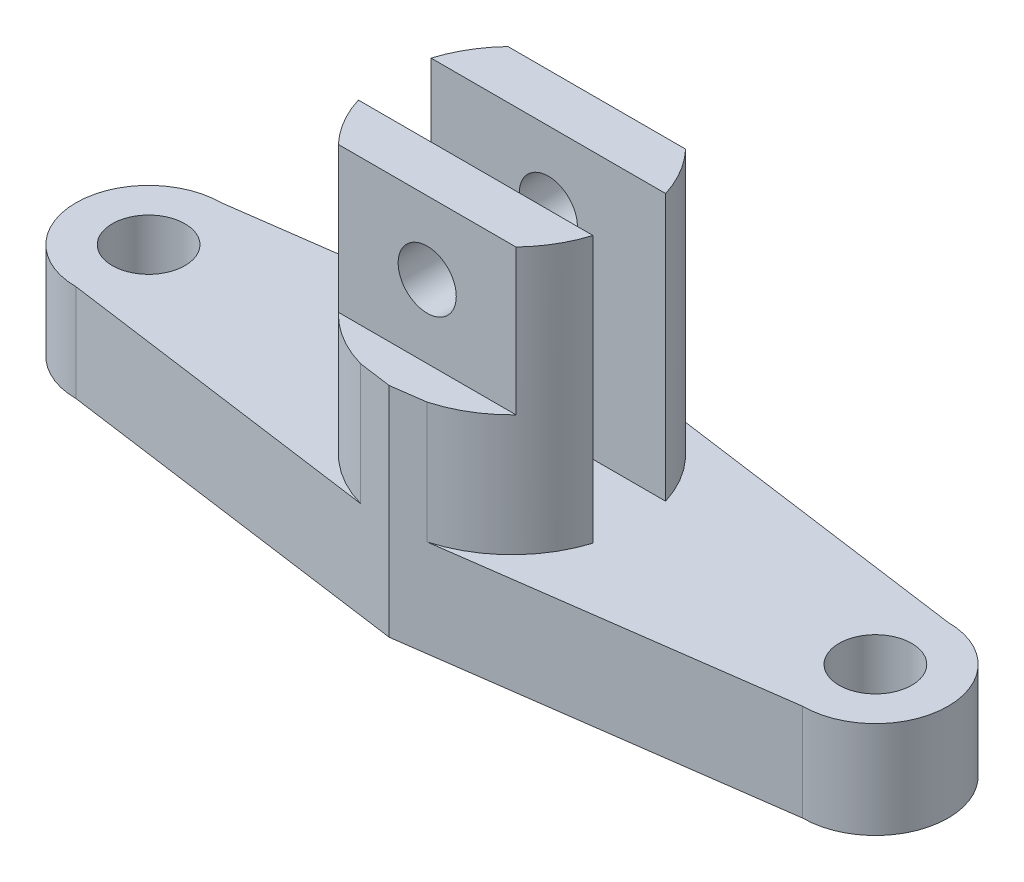
SolidWorks part; units mm, degrees
ref_plane "Alzado" through (0, 0, 0) normal (0, 0, 1) x (1, 0, 0)
ref_plane "Planta" through (0, 0, 0) normal (0, 1, 0) x (1, 0, 0)
ref_plane "Vista lateral" through (0, 0, 0) normal (1, 0, 0) x (0, 0, -1)
sketch "Croquis Planta" plane through (0, 0, 0) normal (0, 1, 0) x (1, 0, 0)
  line L0 (75, 15) -> (0, 25.3396)
  line L1 (0, 25.3396) -> (-75, 15)
  line L2 (0, -25.3396) -> (-75, -15)
  line L3 (0, -25.3396) -> (75, -15)
  circle A0 centre (0, 0) radius 25.3396
  circle A1 centre (75, 0) radius 7.5
  circle A2 centre (-75, 0) radius 7.5
  arc A3 (75, -15) -> (75, 15) centre (75, 0) ccw
  arc A4 (-75, 15) -> (-75, -15) centre (-75, 0) ccw
extrude "Saliente-Extruir1" add sketch "Croquis Planta" along normal blind 20 contours L1 A4 L2 A0 A2 | L3 A3 L0 A0 A1 | L3 A0 L0 L1 L2
sketch "Croquis11" plane through (0, 0, 0) normal (0, 1, 0) x (1, 0, 0)
  line L0 (75, 15) -> (0, 25.3396)
  line L1 (0, 25.3396) -> (-75, 15)
  line L2 (0, -25.3396) -> (-75, -15)
  line L3 (0, -25.3396) -> (75, -15)
  line L4 (-24.2042, 7.5) -> (24.2042, 7.5)
  line L5 (18.326, 17.5) -> (-18.326, 17.5)
  line L6 (-24.2042, -7.5) -> (24.2042, -7.5)
  line L7 (18.326, -17.5) -> (-18.326, -17.5)
  arc A0 (-24.2042, -7.5) -> (24.2042, -7.5) centre (0, 0) ccw
  circle A1 centre (75, 0) radius 7.5
  circle A2 centre (-75, 0) radius 7.5
  arc A3 (75, -15) -> (75, 15) centre (75, 0) ccw
  arc A4 (-75, 15) -> (-75, -15) centre (-75, 0) ccw
  arc A5 (24.2042, 7.5) -> (-24.2042, 7.5) centre (0, 0) ccw
extrude "Saliente-Extruir2" add sketch "Croquis11" along normal blind 45 contours L4 A5 L5 | L5 A5 L0 L1 | L7 A0 L6 | L3 A0 L7 L2
sketch "Croquis12" plane through (0, 0, 0) normal (0, 1, 0) x (1, 0, 0)
  line L0 (75, 15) -> (0, 25.3396)
  line L1 (0, 25.3396) -> (-75, 15)
  line L2 (0, -25.3396) -> (-75, -15)
  line L3 (0, -25.3396) -> (75, -15)
  line L4 (-24.2042, 7.5) -> (24.2042, 7.5)
  line L5 (18.326, 17.5) -> (-18.326, 17.5)
  line L6 (-24.2042, -7.5) -> (24.2042, -7.5)
  line L7 (18.326, -17.5) -> (-18.326, -17.5)
  arc A0 (-24.2042, -7.5) -> (24.2042, -7.5) centre (0, 0) ccw
  circle A1 centre (75, 0) radius 7.5
  circle A2 centre (-75, 0) radius 7.5
  arc A3 (75, -15) -> (75, 15) centre (75, 0) ccw
  arc A4 (-75, 15) -> (-75, -15) centre (-75, 0) ccw
  arc A5 (24.2042, 7.5) -> (-24.2042, 7.5) centre (0, 0) ccw
extrude "Saliente-Extruir3" add sketch "Croquis12" along normal blind 75 contours L4 A5 L5 | L7 A0 L6
sketch "Croquis14" plane through (0, 0, -17.5) normal (0, 0, -1) x (-1, 0, 0)
  circle A0 centre (0, 60) radius 6
  dimension "D1" = 12
extrude "Cortar-Extruir1" cut sketch "Croquis14" against normal through all both and the other way through all
